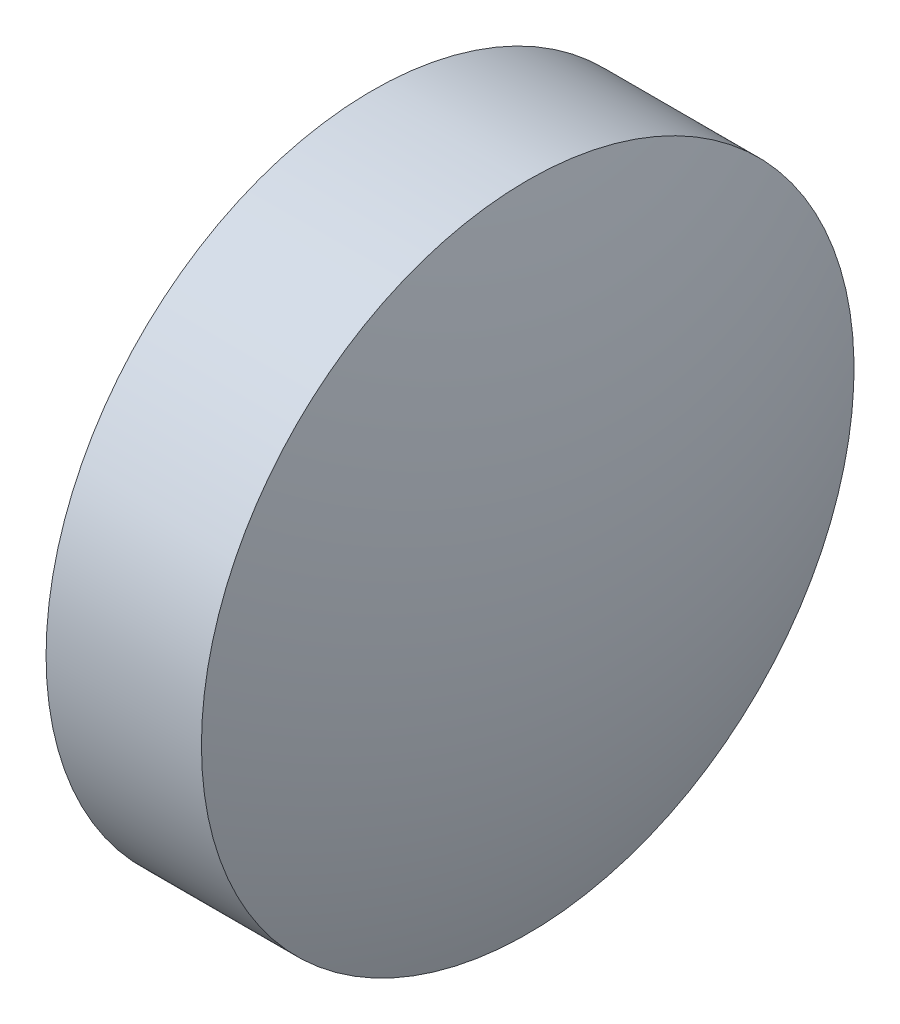
SolidWorks part; units mm, degrees
ref_plane "前视基准面" through (0, 0, 0) normal (0, 0, 1) x (1, 0, 0)
ref_plane "上视基准面" through (0, 0, 0) normal (0, 1, 0) x (1, 0, 0)
ref_plane "右视基准面" through (0, 0, 0) normal (1, 0, 0) x (0, 0, -1)
sketch "草图1" plane through (0, 0, 0) normal (0, 0, 1) x (1, 0, 0)
  line L0 (437.0592, 10.5563) -> (442.4542, 10.5563) construction
  line L1 (437.9198, 10.5563) -> (437.9198, 13.7063)
  line L2 (437.9198, 13.7063) -> (439.4198, 13.7063)
  line L3 (439.9798, 10.5563) -> (437.9198, 10.5563)
  arc A0 (439.9798, 10.5563) -> (439.4198, 13.7063) centre (430.8405, 10.5563) ccw
revolve "旋转1" add sketch "草图1" angle 360 about L0
